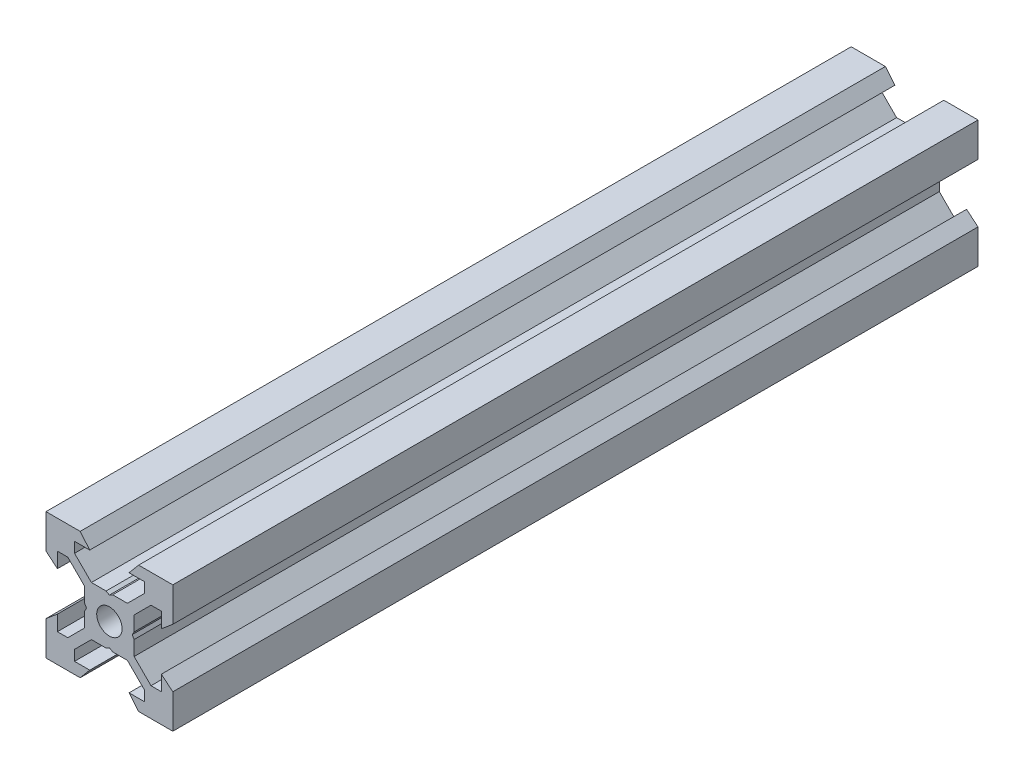
SolidWorks part; units mm, degrees
ref_plane "Front Plane" through (0, 0, 0) normal (0, 0, 1) x (1, 0, 0)
ref_plane "Top Plane" through (0, 0, 0) normal (0, 1, 0) x (1, 0, 0)
ref_plane "Right Plane" through (0, 0, 0) normal (1, 0, 0) x (0, 0, -1)
sketch "Sketch1" plane through (0, 0, 0) normal (0, 0, 1) x (1, 0, 0)
  line L0 (10, 10) -> (4.6104, 10) construction
  line L1 (10, 10) -> (10, 4.6104) construction
  line L2 (10, -10) -> (10, -4.6104) construction
  line L3 (10, -10) -> (4.6104, -10) construction
  line L4 (10, 10) -> (10, 4.6104)
  line L5 (6.5607, 5.5) -> (8.2, 5.5)
  line L6 (5.5, 8.2) -> (5.5, 6.5607)
  line L7 (10, 10) -> (4.6104, 10)
  line L8 (10, 10) -> (10, 4.6104)
  line L9 (6.5607, 5.5) -> (3.9, 2.8393)
  line L10 (5.5, 6.5607) -> (2.8393, 3.9)
  line L11 (10, 4.6104) -> (8.2, 3.1)
  line L12 (4.6104, 10) -> (3.1, 8.2)
  line L13 (8.2, 3.1) -> (8.2, 5.5)
  line L14 (3.1, 8.2) -> (5.5, 8.2)
  line L15 (-6.5607, 5.5) -> (-8.2, 5.5)
  line L16 (6.5607, -5.5) -> (8.2, -5.5)
  line L17 (3.1, -8.2) -> (5.5, -8.2)
  line L18 (8.2, -3.1) -> (8.2, -5.5)
  line L19 (4.6104, -10) -> (3.1, -8.2)
  line L20 (10, -4.6104) -> (8.2, -3.1)
  line L21 (0.5196, -3.9) -> (0, -3.6)
  line L22 (0.5196, 3.9) -> (0, 3.6)
  line L23 (3.6, 0) -> (3.9, -0.5196)
  line L24 (3.9, 0.5196) -> (3.6, 0)
  line L25 (3.9, 0.5196) -> (3.9, 2.8393)
  line L26 (2.8393, 3.9) -> (0.5196, 3.9)
  line L27 (3.9, -2.8393) -> (3.9, -0.5196)
  line L28 (2.8393, -3.9) -> (0.5196, -3.9)
  line L29 (5.5, -6.5607) -> (2.8393, -3.9)
  line L30 (6.5607, -5.5) -> (3.9, -2.8393)
  line L31 (10, -10) -> (10, -4.6104)
  line L32 (10, -10) -> (4.6104, -10)
  line L33 (5.5, -8.2) -> (5.5, -6.5607)
  line L34 (-6.5607, -5.5) -> (-8.2, -5.5)
  line L35 (10, -10) -> (10, -4.6104)
  line L36 (0, 0) -> (0, 8.2) construction
  line L37 (-10, -10) -> (-4.6104, -10) construction
  line L38 (-10, -10) -> (-10, -4.6104) construction
  line L39 (-10, 10) -> (-10, 4.6104) construction
  line L40 (-10, 10) -> (-4.6104, 10) construction
  line L41 (-10, -10) -> (-10, -4.6104)
  line L43 (-5.5, -8.2) -> (-5.5, -6.5607)
  line L44 (-10, -10) -> (-4.6104, -10)
  line L45 (-10, -10) -> (-10, -4.6104)
  line L46 (-6.5607, -5.5) -> (-3.9, -2.8393)
  line L47 (-5.5, -6.5607) -> (-2.8393, -3.9)
  line L48 (-2.8393, -3.9) -> (-0.5196, -3.9)
  line L49 (-3.9, -2.8393) -> (-3.9, -0.5196)
  line L50 (-2.8393, 3.9) -> (-0.5196, 3.9)
  line L51 (-3.9, 0.5196) -> (-3.9, 2.8393)
  line L52 (-3.9, 0.5196) -> (-3.6, 0)
  line L53 (-3.6, 0) -> (-3.9, -0.5196)
  line L54 (-0.5196, 3.9) -> (0, 3.6)
  line L55 (-0.5196, -3.9) -> (0, -3.6)
  line L56 (-10, -4.6104) -> (-8.2, -3.1)
  line L57 (-4.6104, -10) -> (-3.1, -8.2)
  line L58 (-8.2, -3.1) -> (-8.2, -5.5)
  line L59 (-3.1, -8.2) -> (-5.5, -8.2)
  line L60 (-10, -10) -> (10, -10) construction
  line L61 (-10, -10) -> (-10, 10) construction
  line L62 (-3.1, 8.2) -> (-5.5, 8.2)
  line L63 (-8.2, 3.1) -> (-8.2, 5.5)
  line L64 (-4.6104, 10) -> (-3.1, 8.2)
  line L65 (-10, 4.6104) -> (-8.2, 3.1)
  line L66 (-5.5, 6.5607) -> (-2.8393, 3.9)
  line L67 (-6.5607, 5.5) -> (-3.9, 2.8393)
  line L68 (-10, 10) -> (-10, 4.6104)
  line L69 (-10, 10) -> (-4.6104, 10)
  line L70 (-5.5, 8.2) -> (-5.5, 6.5607)
  line L71 (-10, 10) -> (10, 10) construction
  line L72 (-10, 10) -> (-10, 4.6104)
  line L73 (10, -10) -> (10, 10) construction
  line L74 (-10, -10) -> (10, 10) construction
  line L75 (-10, 10) -> (10, -10) construction
  circle A0 centre (0, 0) radius 2
  dimension "D7" = 4
  dimension "D1" = 20
  dimension "D2" = 5.3896
  dimension "D3" = 4.5
  dimension "D4" = 50
  dimension "D5" = 1.8
  dimension "D6" = 1.5104
  dimension "D8" = 5.5
  dimension "D9" = 120
  dimension "D10" = 0.3
  dimension "D11" = 2.3197
  dimension "D12" = 7.8
  dimension "D13" = 7.8
  dimension "D14" = 1.5
  dimension "D15" = 2.6607
extrude "Boss-Extrude1" add sketch "Sketch1" along normal mid plane 127 contours L70 L62 L64 L69 L68 L65 L63 L15 L67 L51 L52 L53 L49 L46 L34 L58 L56 L41 L44 L57 L59 L43 L47 L48 L55 L21 L28 L29 L33 L17 L19 L32 L31 L20 L18 L16 L30 L27 L23 L24 L25 L9 L5 L13 L11 L4 L7 L12 L14 L6 L10
